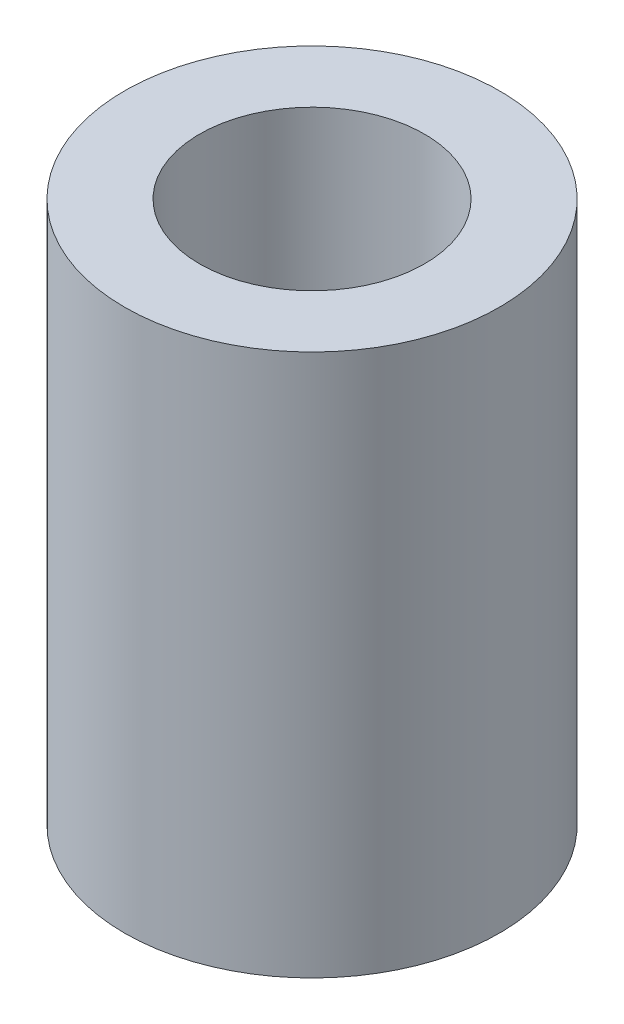
SolidWorks part; units mm, degrees
ref_plane "前视基准面" through (0, 0, 0) normal (0, 0, 1) x (1, 0, 0)
ref_plane "上视基准面" through (0, 0, 0) normal (0, 1, 0) x (1, 0, 0)
ref_plane "右视基准面" through (0, 0, 0) normal (1, 0, 0) x (0, 0, -1)
sketch "草图1" plane through (0, 0, 0) normal (0, 1, 0) x (1, 0, 0)
  circle A0 centre (0, 0) radius 2.5
  circle A1 centre (0, 0) radius 1.5
  dimension "D1" = 3
  dimension "D2" = 5
extrude "凸台-拉伸1" add sketch "草图1" along normal blind 7.23
